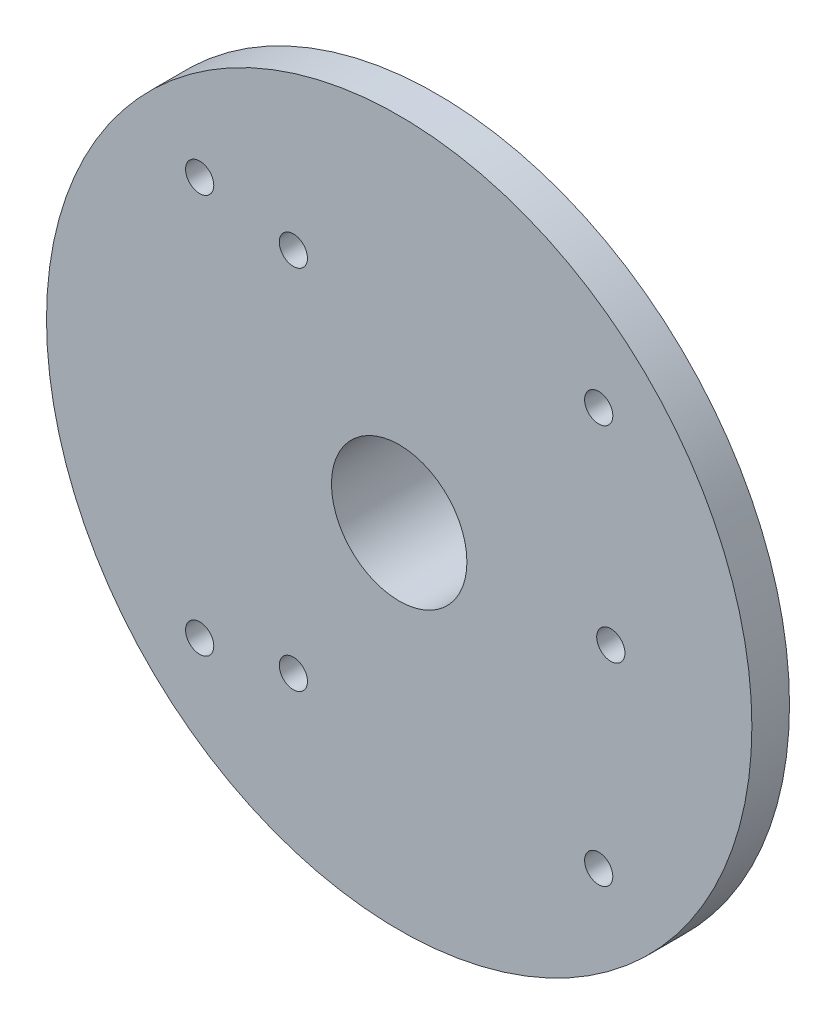
SolidWorks part; units mm, degrees
ref_plane "Front Plane" through (0, 0, 0) normal (0, 0, 1) x (1, 0, 0)
ref_plane "Top Plane" through (0, 0, 0) normal (0, 1, 0) x (1, 0, 0)
ref_plane "Right Plane" through (0, 0, 0) normal (1, 0, 0) x (0, 0, -1)
sketch "Sketch1" plane through (0, 0, 0) normal (0, 0, 1) x (1, 0, 0)
  line L0 (0, 0) -> (125, 0) construction
  line L1 (0, 0) -> (21.2132, 21.2132) construction
  line L25 (125, 0) -> (127.5, 0) construction
  line L27 (0, 0) -> (0, -15) construction
  circle A0 centre (0, 0) radius 37.5
  circle A3 centre (0, 0) radius 7.2
  circle A26 centre (0, 0) radius 10 construction
  circle A27 centre (0, 0) radius 22.5 construction
  circle A38 centre (22.5, 0) radius 1.5
  circle A39 centre (-11.25, -19.4856) radius 1.5
  circle A40 centre (-11.25, 19.4856) radius 1.5
  circle A47 centre (0, 0) radius 30 construction
  circle A48 centre (21.2132, 21.2132) radius 1.5
  circle A49 centre (21.2132, -21.2132) radius 1.5
  circle A50 centre (-21.2132, -21.2132) radius 1.5
  circle A51 centre (-21.2132, 21.2132) radius 1.5
  point P11 (0, 0)
  point P14 (0, 0)
  point P22 (0, 0)
  point P26 (0, 0)
  point P28 (0, 0)
  point P46 (0, 77.5)
  point P53 (54.8008, 54.8008)
  point P65 (0, 0)
  point P78 (0, 0)
  point P84 (0, 0)
  point P86 (0, 0)
  point P87 (-54.8008, 54.8008)
  dimension "D1" = 75
  dimension "D2" = 3
  dimension "D3" = 20
  dimension "D4" = 14.4
  dimension "D5" = 3
  dimension "D8" = 3
  dimension "D9" = 45
  dimension "D10" = 4
  dimension "D6" = 45
  dimension "D7" = 60
extrude "Boss-Extrude1" add sketch "Sketch1" along normal blind 4
sketch "Sketch2" plane through (0, 0, 0) normal (0, 0, -1) x (-1, 0, 0)
  circle A1 centre (0, 0) radius 11.2
  circle A10 centre (0, 0) radius 7.2 construction
  circle A11 centre (0, 0) radius 7.2 construction
  circle A12 centre (0, 0) radius 7.2
  dimension "D1" = 22.4
  dimension "D2" = 14.4
extrude "Boss-Extrude2" add sketch "Sketch2" along normal blind 8
